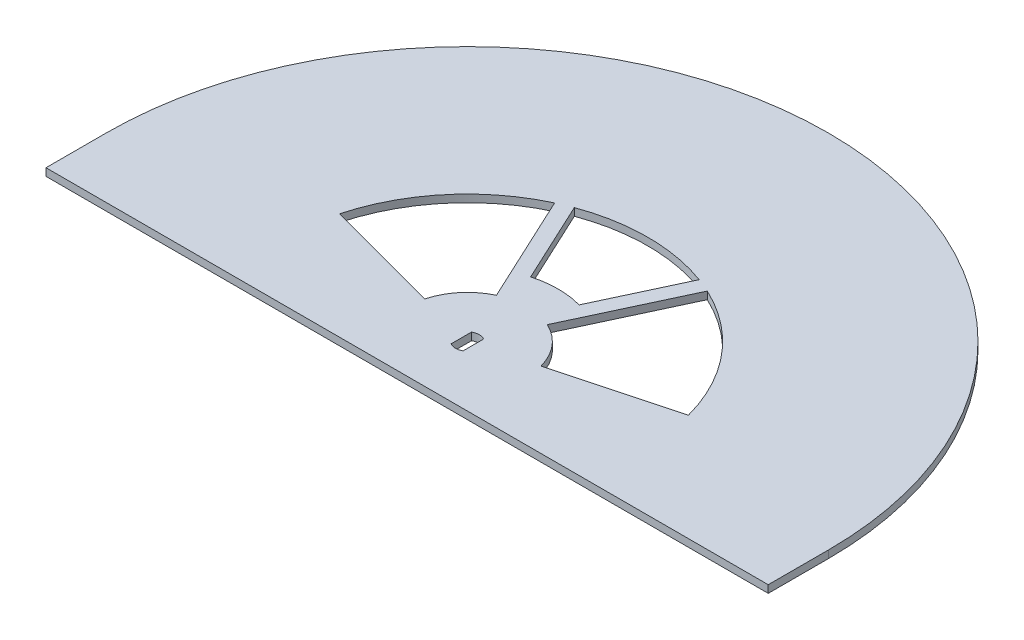
SolidWorks part; units mm, degrees
ref_plane "Front Plane" through (0, 0, 0) normal (0, 0, 1) x (1, 0, 0)
ref_plane "Top Plane" through (0, 0, 0) normal (0, 1, 0) x (1, 0, 0)
ref_plane "Right Plane" through (0, 0, 0) normal (1, 0, 0) x (0, 0, -1)
sketch "Sketch1" plane through (0, 0, 0) normal (0, 1, 0) x (1, 0, 0)
  line L0 (-76.2, 0) -> (76.2, 0)
  line L1 (0, 76.2) -> (0, 0) construction
  line L2 (0, 0) -> (0, 57.15) construction
  line L3 (0, 0) -> (24.1526, 51.7955) construction
  line L4 (0, 0) -> (0, 57.15) construction
  line L5 (0, 0) -> (-24.1526, 51.7955) construction
  line L6 (-55.2027, 14.7915) -> (0, 0) construction
  line L7 (-43.7794, 36.7353) -> (0, 0) construction
  line L8 (43.7794, 36.7353) -> (0, 0) construction
  line L9 (55.2027, 14.7915) -> (0, 0) construction
  line L10 (-12.2673, 3.287) -> (-36.8018, 9.861)
  line L11 (-16.1018, 34.5303) -> (-5.3673, 11.5101)
  line L12 (36.8018, 9.861) -> (12.2673, 3.287)
  line L13 (5.3673, 11.5101) -> (16.1018, 34.5303)
  line L14 (-13.1682, 35.752) -> (-5.1173, 18.4869)
  line L15 (13.1682, 35.752) -> (5.1173, 18.4869)
  arc A0 (76.2, 0) -> (-76.2, 0) centre (0, 0) ccw
  arc A4 (-57.15, 0) -> (57.15, 0) centre (0, 0) cw construction
  circle A5 centre (0, 57.15) radius 9.525 construction
  circle A6 centre (24.1526, 51.7955) radius 9.525 construction
  circle A7 centre (43.7794, 36.7353) radius 9.525 construction
  circle A8 centre (55.2027, 14.7915) radius 9.525 construction
  circle A9 centre (-24.1526, 51.7955) radius 9.525 construction
  circle A10 centre (-43.7794, 36.7353) radius 9.525 construction
  circle A11 centre (-55.2027, 14.7915) radius 9.525 construction
  arc A12 (-38.1, 0) -> (38.1, 0) centre (0, 0) cw construction
  arc A13 (-12.7, 0) -> (12.7, 0) centre (0, 0) cw construction
  arc A14 (-12.2673, 3.287) -> (-5.3673, 11.5101) centre (0, 0) cw
  arc A15 (-36.8018, 9.861) -> (-16.1018, 34.5303) centre (0, 0) cw
  arc A16 (16.1018, 34.5303) -> (36.8018, 9.861) centre (0, 0) cw
  arc A17 (5.3673, 11.5101) -> (12.2673, 3.287) centre (0, 0) cw
  arc A18 (-5.1173, 18.4869) -> (5.1173, 18.4869) centre (0, 0) cw
  arc A19 (-13.1682, 35.752) -> (13.1682, 35.752) centre (0, 0) cw
  point P45 (0, 0)
  dimension "D1" = 152.4
  dimension "D6" = 19.05
  dimension "D9" = 4
  dimension "D10" = 2
  dimension "D11" = 19.05
  dimension "D12" = 3.175
  dimension "D7" = 4
extrude "Boss-Extrude1" add sketch "Sketch1" along normal blind 1.5875
sketch "Sketch2" plane through (0, 1.5875, 0) normal (0, 1, 0) x (1, 0, 0)
  line L0 (0, 0) -> (0, 57.15) construction
  line L1 (0, 0) -> (24.1526, 51.7955) construction
  circle A0 centre (0, 0) radius 57.15 construction
  arc A1 (57.15, 0) -> (-57.15, 0) centre (0, 0) ccw construction
  circle A2 centre (0, 57.15) radius 9.525
  circle A3 centre (0, 57.15) radius 9.525 construction
  circle A4 centre (24.1526, 51.7955) radius 9.525
  circle A5 centre (43.7794, 36.7353) radius 9.525
  circle A6 centre (55.2027, 14.7915) radius 9.525
  circle A7 centre (-24.1526, 51.7955) radius 9.525
  circle A8 centre (-43.7794, 36.7353) radius 9.525
  circle A9 centre (-55.2027, 14.7915) radius 9.525
  circle A10 centre (-55.2027, 14.7915) radius 7.9375
  circle A13 centre (0, 57.15) radius 7.9375
  circle A14 centre (24.1526, 51.7955) radius 7.9375
  circle A15 centre (43.7794, 36.7353) radius 7.9375
  circle A16 centre (55.2027, 14.7915) radius 7.9375
  circle A17 centre (-43.7794, 36.7353) radius 7.9375
  circle A18 centre (-24.1526, 51.7955) radius 7.9375
  point P27 (0, 0)
  dimension "D4" = 1.5875
  dimension "D2" = 25
  dimension "D1" = 4
  dimension "D3" = 4
extrude "Boss-Extrude2" [suppressed] add sketch "Sketch2" along normal blind 6.35
fillet "Fillet1" [suppressed] radius 2.54
fillet "Fillet2" [suppressed] radius 2.54
fillet "Fillet3" [suppressed] radius 2.54
fillet "Fillet4" [suppressed] radius 2.54
fillet "Fillet5" [suppressed] radius 2.54
fillet "Fillet6" [suppressed] radius 2.54
fillet "Fillet7" [suppressed] radius 2.54
sketch "Sketch3" plane through (0, 1.5875, 0) normal (0, 1, 0) x (1, 0, 0)
  line L0 (-76.2, 0) -> (76.2, 0) construction
  line L1 (-76.2, 0) -> (76.2, 0)
  line L2 (-76.2, 0) -> (-76.2, -12.7)
  line L3 (-76.2, -12.7) -> (76.2, -12.7)
  line L4 (76.2, 0) -> (76.2, -12.7)
  point P6 (0, 0)
  point P7 (0, 0)
  point P8 (-39.4706, 0)
  point P9 (-39.4706, 0)
  point P10 (-39.4706, 0)
  point P11 (-76.2, 0)
  dimension "D1" = 12.7
extrude "Boss-Extrude3" add sketch "Sketch3" against normal blind 1.5875
sketch "Sketch4" plane through (0, 1.5875, 0) normal (0, 1, 0) x (1, 0, 0)
  line L0 (-1.2757, 2.15) -> (-1.2757, -2.15)
  line L1 (1.2757, 2.15) -> (1.2757, -2.15)
  arc A0 (-1.2757, -2.15) -> (1.2757, -2.15) centre (0, 0) ccw
  arc A1 (1.2757, 2.15) -> (-1.2757, 2.15) centre (0, 0) ccw
  dimension "D1" = 5
  dimension "D2" = 4.3
extrude "Cut-Extrude1" cut sketch "Sketch4" against normal through all
